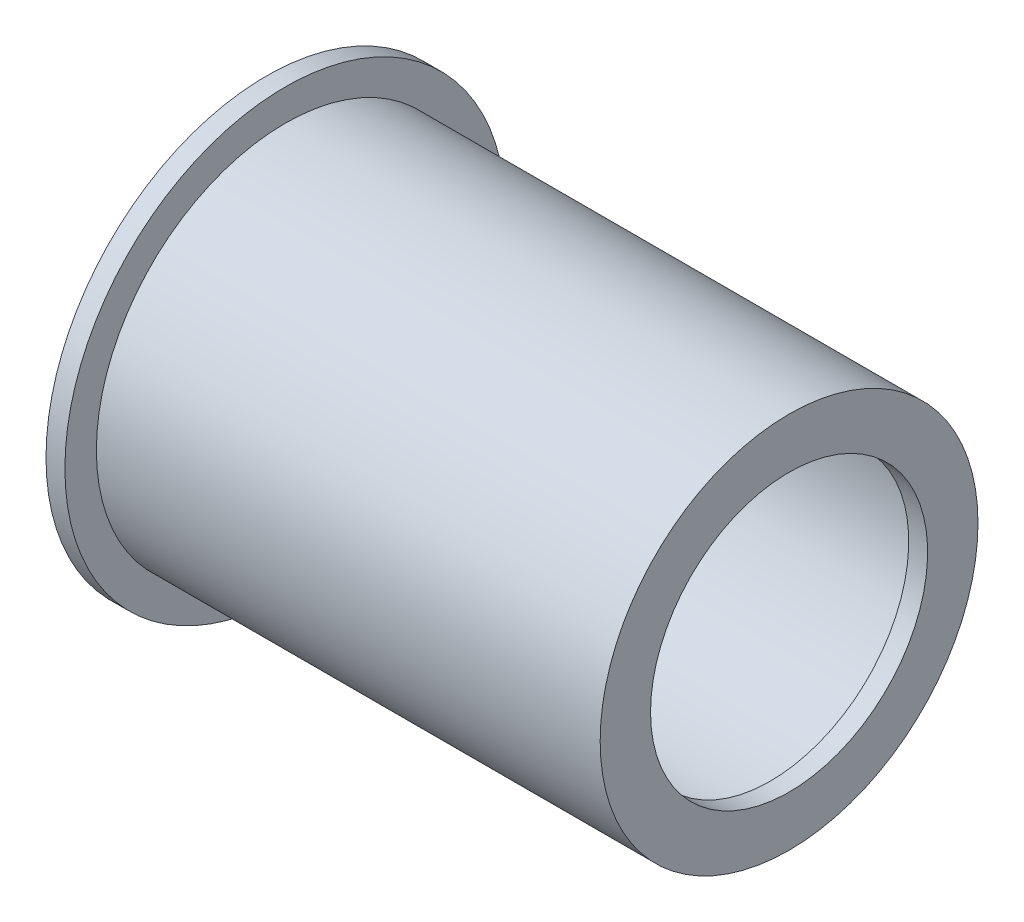
SolidWorks part; units mm, degrees
ref_plane "Front Plane" through (0, 0, 0) normal (0, 0, 1) x (1, 0, 0)
ref_plane "Top Plane" through (0, 0, 0) normal (0, 1, 0) x (1, 0, 0)
ref_plane "Right Plane" through (0, 0, 0) normal (1, 0, 0) x (0, 0, -1)
sketch "Sketch1" plane through (0, 0, 0) normal (0, 0, 1) x (1, 0, 0)
  line L0 (8.2184, 35) -> (8.2184, 27)
  line L1 (8.2184, 27) -> (88.2184, 27)
  line L2 (88.2184, 27) -> (88.2184, 22)
  line L3 (0, 0) -> (84.1526, 0) construction
  line L4 (14.2184, 30) -> (11.2184, 30) construction
  line L5 (11.2184, 35) -> (11.2184, -35) construction
  line L6 (11.2184, 35) -> (-65.7816, 35) construction
  dimension "D1" = 3
  dimension "D2" = 3
  dimension "D3" = 5
  dimension "D4" = 80
revolve "Revolve-Thin1" add sketch "Sketch1" angle 360 about L3 wall 3
sketch "Sketch2" plane through (8.2184, 0, 0) normal (-1, 0, 0) x (0, 0, 1)
  circle A0 centre (0, 0) radius 27
extrude "Boss-Extrude1" add sketch "Sketch2" against normal blind 3
